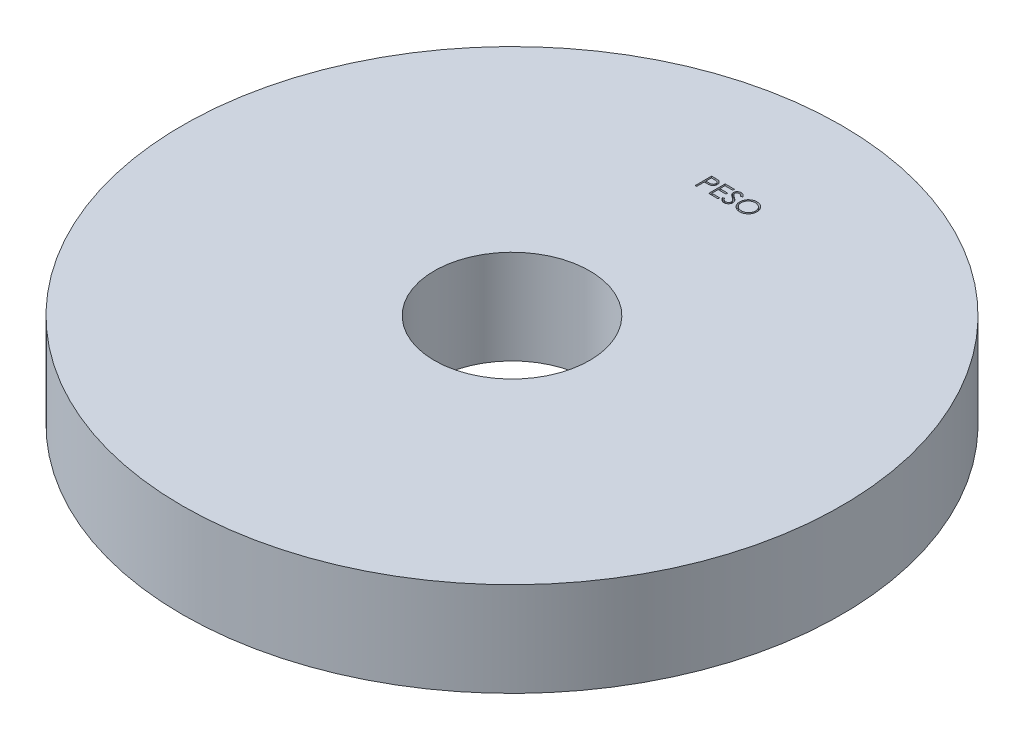
SolidWorks part; units mm, degrees
ref_plane "Plano frontal" through (0, 0, 0) normal (0, 0, 1) x (1, 0, 0)
ref_plane "Plano superior" through (0, 0, 0) normal (0, 1, 0) x (1, 0, 0)
ref_plane "Plano direito" through (0, 0, 0) normal (1, 0, 0) x (0, 0, -1)
sketch "Esboço1" plane through (0, 0, 0) normal (0, 1, 0) x (1, 0, 0)
  circle A0 centre (0, 0) radius 70
  circle A1 centre (0, 0) radius 16.5
  dimension "D1" = 33
  dimension "D2" = 140
extrude "Ressalto-extrusão1" add sketch "Esboço1" along normal blind 20
sketch "Esboço2" plane through (0, 20, 0) normal (0, 1, 0) x (1, 0, 0)
  text T0 "PESO"
extrude "Corte-extrusão1" cut sketch "Esboço2" against normal blind 1
